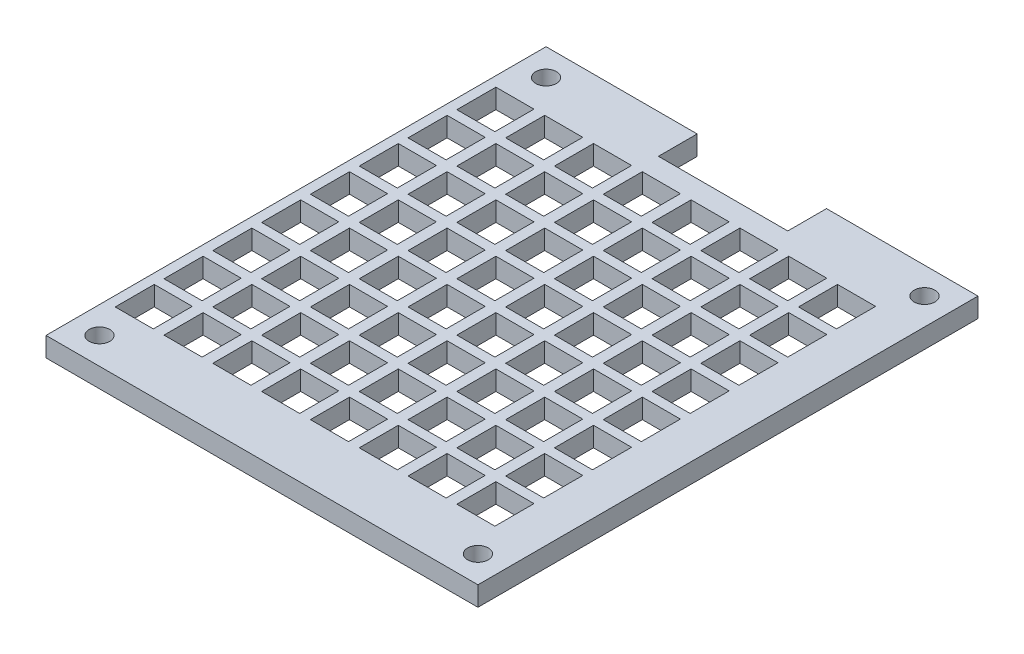
SolidWorks part; units mm, degrees
ref_plane "Front" through (0, 0, 0) normal (0, 0, 1) x (1, 0, 0)
ref_plane "Top" through (0, 0, 0) normal (0, 1, 0) x (1, 0, 0)
ref_plane "Right" through (0, 0, 0) normal (1, 0, 0) x (0, 0, -1)
sketch "Sketch1" plane through (0, 0, 0) normal (0, 1, 0) x (1, 0, 0)
  line L0 (36.4871, 65.0621) -> (36.4871, 60.0202)
  line L1 (0, 0) -> (56.1975, 0)
  line L2 (0, 0) -> (0, 65.0621)
  line L3 (0, 65.0621) -> (56.1975, 65.0621)
  line L4 (56.1975, 0) -> (56.1975, 65.0621)
  line L5 (36.4871, 60.0202) -> (19.6596, 60.0202)
  line L6 (19.6596, 60.0202) -> (19.6596, 65.0621)
  line L7 (3.4798, 61.5823) -> (3.4798, 3.4798) construction
  line L8 (3.4798, 3.4798) -> (52.7177, 3.4798) construction
  line L9 (52.7177, 3.4798) -> (52.7177, 61.5823) construction
  line L10 (52.7177, 61.5823) -> (3.4798, 61.5823) construction
  circle A0 centre (3.4798, 61.5823) radius 1.3462
  circle A1 centre (52.7177, 61.5823) radius 1.3462
  circle A2 centre (52.7177, 3.4798) radius 1.3462
  circle A3 centre (3.4798, 3.4798) radius 1.3462
  dimension "D6" = 2.6924
  dimension "D7" = 2.1336
  dimension "D8" = 2.1336
  dimension "D9" = 2.1336
  dimension "D10" = 2.1336
  dimension "D1" = 56.1975
  dimension "D2" = 65.0621
  dimension "D3" = 19.7104
  dimension "D4" = 16.8275
  dimension "D5" = 5.0419
extrude "Boss-Extrude1" add sketch "Sketch1" along normal blind 2.54 contours L5 L6 L3 L2 L1 L4 L0 A3 A2 A1 A0
sketch "Sketch2" plane through (0, 2.54, 0) normal (0, 1, 0) x (1, 0, 0)
  line L0 (0, 65.0621) -> (19.6596, 65.0621) construction
  line L1 (1.2954, 57.2389) -> (6.2484, 57.2389)
  line L2 (1.2954, 57.2389) -> (1.2954, 52.1589)
  line L3 (1.2954, 52.1589) -> (6.2484, 52.1589)
  line L4 (6.2484, 57.2389) -> (6.2484, 52.1589)
  line L5 (0, 0) -> (0, 65.0621) construction
  dimension "D1" = 7.8232
  dimension "D2" = 1.2954
  dimension "D3" = 4.953
  dimension "D4" = 5.08
extrude "Cut-Extrude1" cut sketch "Sketch2" against normal through all
pattern_linear "LPattern1" count 8 spacing 6.35 along (1, 0, 0) count 8 spacing 6.35 along (0, 0, 1) of "Cut-Extrude1"
